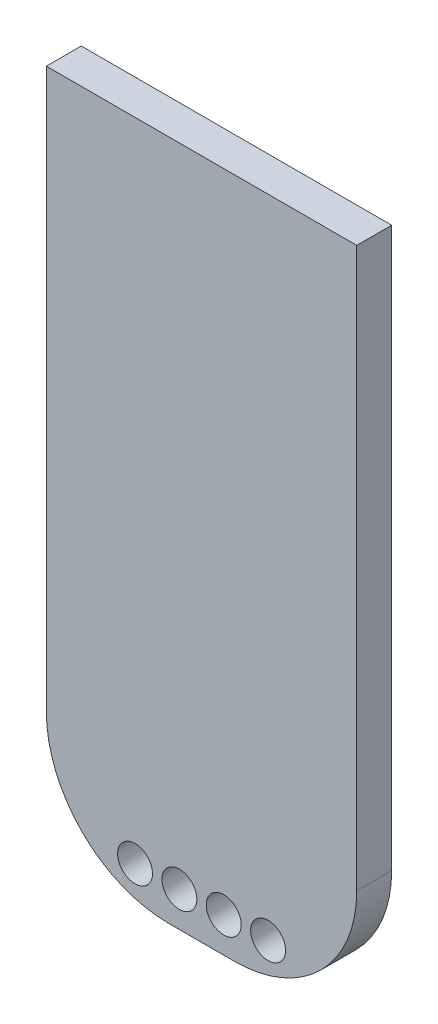
SolidWorks part; units mm, degrees
ref_plane "Front Plane" through (0, 0, 0) normal (0, 0, 1) x (1, 0, 0)
ref_plane "Top Plane" through (0, 0, 0) normal (0, 1, 0) x (1, 0, 0)
ref_plane "Right Plane" through (0, 0, 0) normal (1, 0, 0) x (0, 0, -1)
sketch "Sketch1" plane through (0, 0, 0) normal (0, 0, 1) x (1, 0, 0)
  line L1 (0, 39.02) -> (17.78, 39.02)
  line L2 (0, 39.02) -> (0, 0)
  line L3 (0, 0) -> (17.78, 0)
  line L4 (17.78, 39.02) -> (17.78, 0)
  dimension "D1" = 17.78
  dimension "D2" = 39.02
  dimension "D3" = 0
extrude "Boss-Extrude1" add sketch "Sketch1" along normal blind 2
sketch "Sketch2" plane through (0, 0, 2) normal (0, 0, 1) x (1, 0, 0)
  line L0 (7.6213, 2) -> (10.1613, 2)
  line L1 (0, 0) -> (17.78, 0) construction
  circle A0 centre (5.0813, 2) radius 1
  circle A1 centre (7.6213, 2) radius 1
  circle A2 centre (10.1613, 2) radius 1
  circle A3 centre (12.7013, 2) radius 1
  dimension "D1" = 2
  dimension "D2" = 2.54
  dimension "D3" = 2.54
  dimension "D4" = 2.54
  dimension "D5" = 2
extrude "Cut-Extrude5" cut sketch "Sketch2" against normal blind 10
fillet "Fillet4" radius 7 2 edges at (17.78, 0, 1) (0, 0, 1)
